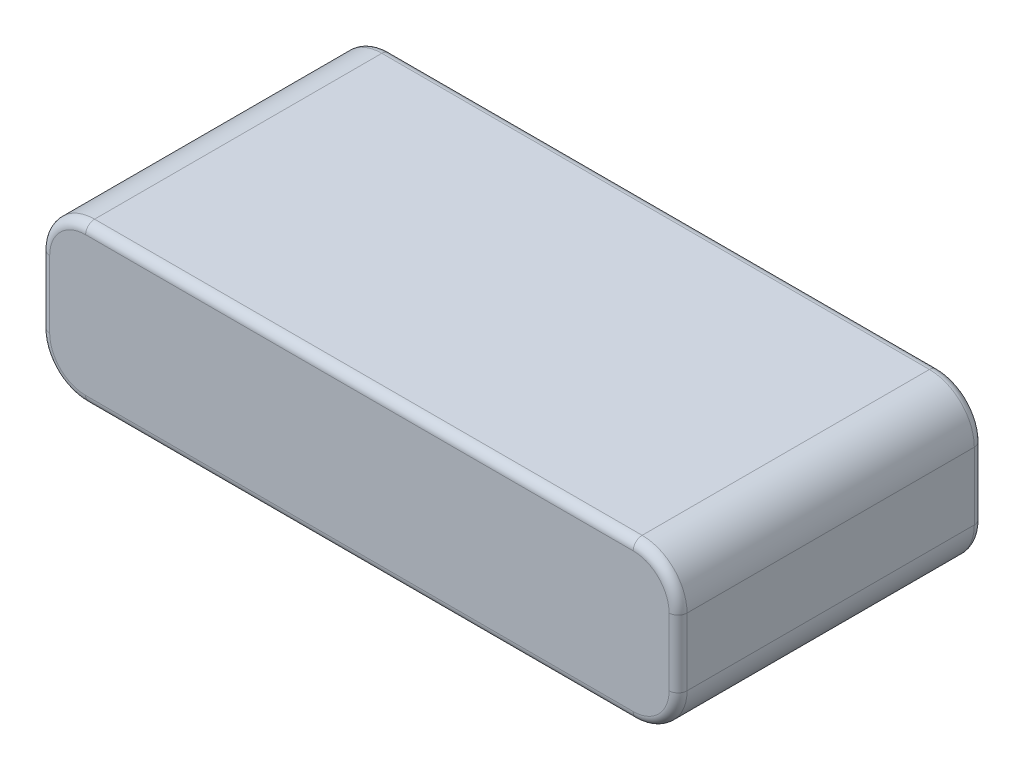
SolidWorks part; units mm, degrees
ref_plane "Front Plane" through (0, 0, 0) normal (0, 0, 1) x (1, 0, 0)
ref_plane "Top Plane" through (0, 0, 0) normal (0, 1, 0) x (1, 0, 0)
ref_plane "Right Plane" through (0, 0, 0) normal (1, 0, 0) x (0, 0, -1)
sketch "Sketch2" plane through (0, 0, 0) normal (0, 1, 0) x (1, 0, 0)
  line L1 (-35.5, 17) -> (35.5, 17)
  line L2 (-35.5, 17) -> (-35.5, -17)
  line L3 (-35.5, -17) -> (35.5, -17)
  line L4 (35.5, 17) -> (35.5, -17)
  line L5 (-35.5, 17) -> (35.5, -17) construction
  line L6 (-35.5, -17) -> (35.5, 17) construction
  point P0 (0, 0)
  dimension "D1" = 71
  dimension "D2" = 34
extrude "Boss-Extrude1" add sketch "Sketch2" along normal blind 17.5
fillet "Fillet1" radius 5 4 edges at (35.5, 17.5, 0) (35.5, 0, 0) (-35.5, 0, 0) (-35.5, 17.5, 0)
fillet "Fillet2" radius 1 16 edges at (34.0355, 1.4645, 17) (0, 0, 17) (-34.0355, 1.4645, 17) (-35.5, 8.75, 17) (-34.0355, 16.0355, 17) (0, 17.5, 17) (34.0355, 16.0355, 17) (35.5, 8.75, 17) (-34.0355, 16.0355, -17) (-35.5, 8.75, -17) (-34.0355, 1.4645, -17) (0, 0, -17) (34.0355, 1.4645, -17) (35.5, 8.75, -17) (34.0355, 16.0355, -17) (0, 17.5, -17)
